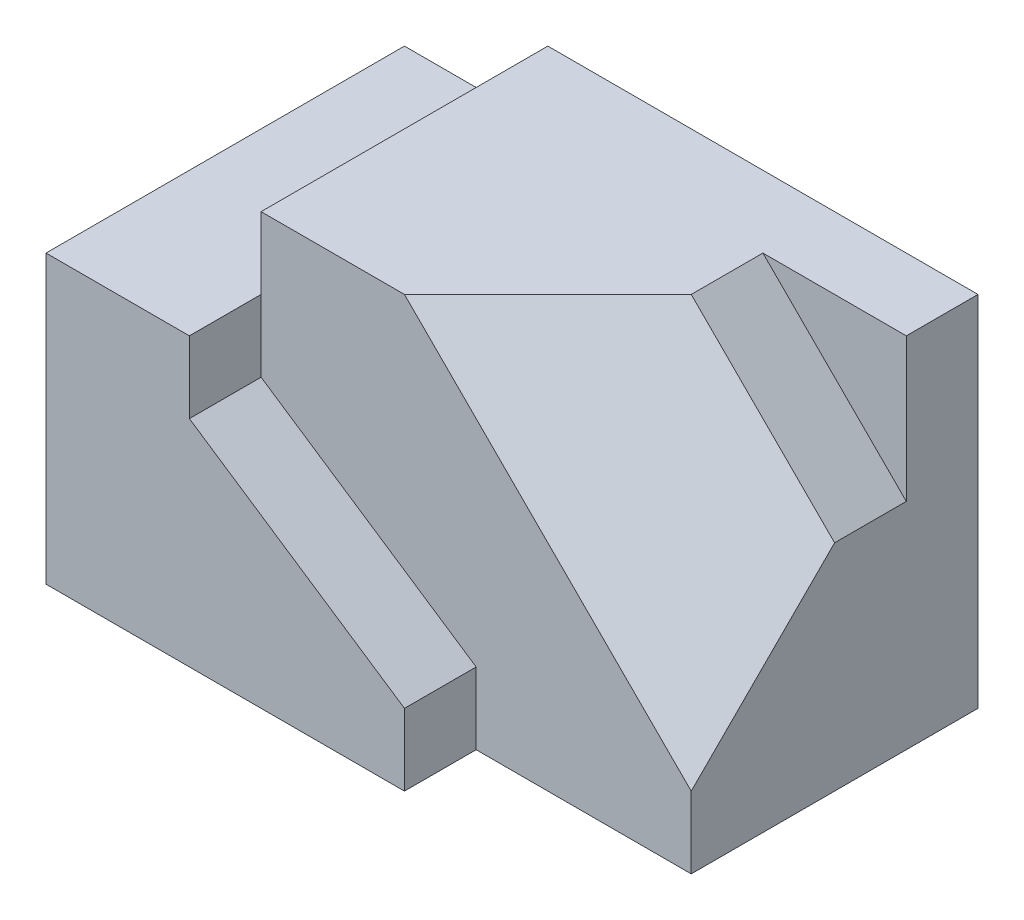
SolidWorks part; units mm, degrees
ref_plane "Front Plane" through (0, 0, 0) normal (0, 0, 1) x (1, 0, 0)
ref_plane "Top Plane" through (0, 0, 0) normal (0, 1, 0) x (1, 0, 0)
ref_plane "Right Plane" through (0, 0, 0) normal (1, 0, 0) x (0, 0, -1)
sketch "Sketch2" plane through (0, 0, 0) normal (0, 1, 0) x (1, 0, 0)
  line L1 (0, 0) -> (80, 0)
  line L2 (0, 0) -> (0, 50)
  line L3 (0, 50) -> (80, 50)
  line L4 (80, 0) -> (80, 50)
  dimension "D1" = 80
  dimension "D2" = 50
extrude "Boss-Extrude1" add sketch "Sketch2" along normal blind 10
sketch "Sketch3" plane through (0, 10, 0) normal (0, 1, 0) x (1, 0, 0)
  line L1 (80, 0) -> (50, 0)
  line L2 (80, 0) -> (80, 10)
  line L3 (80, 10) -> (50, 10)
  line L4 (50, 0) -> (50, 10)
  dimension "D1" = 30
  dimension "D2" = 10
extrude "Cut-Extrude1" cut sketch "Sketch3" against normal blind 10
sketch "Sketch4" plane through (0, 10, 0) normal (0, 1, 0) x (1, 0, 0)
  line L1 (80, 50) -> (20, 50)
  line L2 (80, 50) -> (80, 10)
  line L3 (80, 10) -> (20, 10)
  line L4 (20, 50) -> (20, 10)
  dimension "D1" = 60
  dimension "D2" = 40
extrude "Boss-Extrude2" add sketch "Sketch4" along normal blind 40
sketch "Sketch5" plane through (0, 0, 0) normal (0, 0, 1) x (1, 0, 0)
  line L0 (0, 10) -> (0, 40)
  line L1 (0, 40) -> (20, 40)
  line L2 (20, 40) -> (20, 30)
  line L3 (20, 30) -> (50, 10)
  line L5 (50, 10) -> (0, 10)
  line M3 (50, 10) -> (0, 10)
  dimension "D1" = 30
  dimension "D2" = 20
  dimension "D3" = 10
  dimension "D4" = 20
  dimension "D5" = 30
extrude "Boss-Extrude3" add sketch "Sketch5" against normal blind 50 contours L3 L2 L1 L0 M3
ref_plane "Plane1" through (0, 0, -40) normal (0, 0, 1) x (1, 0, 0)
sketch "Sketch6" plane through (0, 0, -40) normal (0, 0, 1) x (1, 0, 0)
  line L0 (60, 50) -> (80, 30)
  line L1 (20, 50) -> (80, 50) construction
  line L2 (80, 0) -> (80, 50) construction
  line L3 (80, 30) -> (80, 50)
  line L4 (80, 50) -> (60, 50)
  dimension "D1" = 20
  dimension "D2" = 20
extrude "Cut-Extrude2" cut sketch "Sketch6" along normal blind 50
sketch "Sketch7" plane through (0, 0, -10) normal (0, 0, 1) x (1, 0, 0)
  line L0 (20, 50) -> (60, 50) construction
  line L3 (80, 0) -> (80, 30) construction
  point P0 (40, 50)
  point P1 (80, 10)
  dimension "D1" = 20
  dimension "D2" = 10
sketch "Sketch8" plane through (55, 55, 0) normal (0.7071, 0.7071, 0) x (0, 0, -1)
  line L0 (40, -7.0711) -> (10, -7.0711) construction
  line L1 (40, 27.5) -> (40, -27.5) construction
  point P0 (30, -7.0711)
  dimension "D1" = 10
ref_plane "Plane2" through (26.6667, 26.6667, 26.6667) normal (-0.5774, -0.5774, -0.5774) x (-0.8165, 0.4082, 0.4082)
sketch "Sketch9" plane through (26.6667, 26.6667, 26.6667) normal (-0.5774, -0.5774, -0.5774) x (-0.8165, 0.4082, 0.4082)
  line L0 (-16.3299, 42.4264) -> (-40.8248, 56.5685)
  line L1 (-40.8248, 56.5685) -> (-65.3197, 42.4264)
  line L2 (-65.3197, 42.4264) -> (-65.3197, 14.1421)
  line L3 (-65.3197, 14.1421) -> (-16.3299, 42.4264)
  line L4 (-44.9073, 63.6396) -> (-69.4022, 49.4975) construction
extrude "Cut-Extrude3" cut sketch "Sketch9" against normal blind 50
